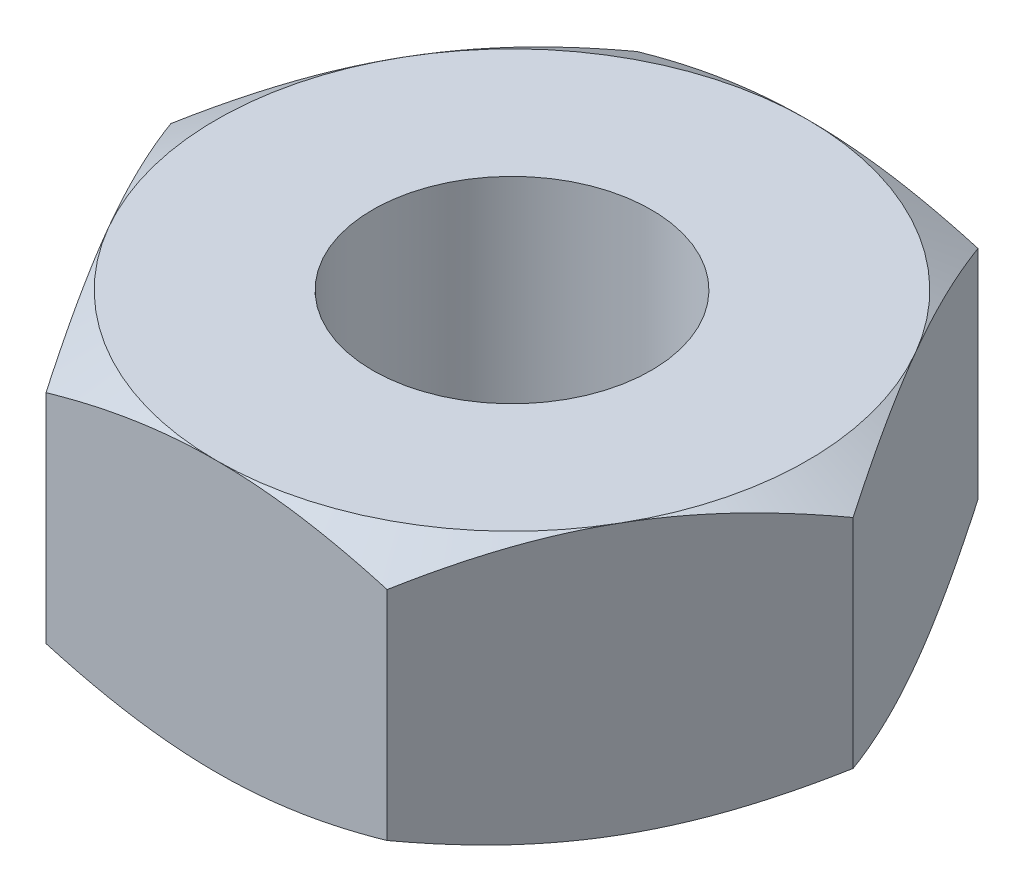
SolidWorks part; units mm, degrees
ref_plane "Front Plane" through (0, 0, 0) normal (0, 0, 1) x (1, 0, 0)
ref_plane "Top Plane" through (0, 0, 0) normal (0, 1, 0) x (1, 0, 0)
ref_plane "Right Plane" through (0, 0, 0) normal (1, 0, 0) x (0, 0, -1)
sketch "Sketch1" plane through (0, 0, 0) normal (0, 1, 0) x (1, 0, 0)
  line L1 (-2.0207, -3.5) -> (2.0207, -3.5)
  line L2 (2.0207, -3.5) -> (4.0415, 0)
  line L3 (4.0415, 0) -> (2.0207, 3.5)
  line L4 (2.0207, 3.5) -> (-2.0207, 3.5)
  line L5 (-2.0207, 3.5) -> (-4.0415, 0)
  line L6 (-4.0415, 0) -> (-2.0207, -3.5)
  circle A0 centre (0, 0) radius 3.5 construction
  dimension "D1" = 7
extrude "Boss-Extrude1" add sketch "Sketch1" along normal blind 3.2
sketch "Sketch2" plane through (0, 0, 0) normal (1, 0, 0) x (0, 0, -1)
  line L0 (0, 0) -> (0, 3.5465) construction
  line L1 (5.6272, 1.2282) -> (3.5, 0)
  line L2 (3.5, 3.2) -> (5.6447, 3.2)
  line L5 (5.6447, 3.2) -> (5.6447, 1.9617)
  line L6 (3.5, 0) -> (5.6272, 0)
  line L9 (5.6272, 0) -> (5.6272, 1.2282)
  line L10 (5.6447, 1.9617) -> (3.5, 3.2)
  dimension "D1" = 30
  dimension "D2" = 30
revolve "Cut-Revolve1" cut sketch "Sketch2" angle 360 about L0
hole_wizard "M4 Tapped Hole1" positions "3DSketch2" profile "Sketch3" tap size "M4" standard "DIN" end condition through all
sketch3d "3DSketch2"
  point P0 (0, 3.2, 0)
sketch "Sketch3" plane through (0, 3.2, 0) normal (1, 0, 0) x (0, 0, 1)
  line L0 (0, 0) -> (0, 3.2)
  line L1 (0, 3.2) -> (1.65, 3.2)
  line L2 (1.65, 3.2) -> (1.65, 0)
  line L5 (1.65, 0) -> (0, 0)
  line L11 (0, -6.35) -> (0, 107.95) construction
  dimension "Thru Tap Drill Dia." = 3.3
  dimension "Thru Tap Drill Depth" = 3.2
cosmetic thread "Hole Thread1" parameters "D2"=4
